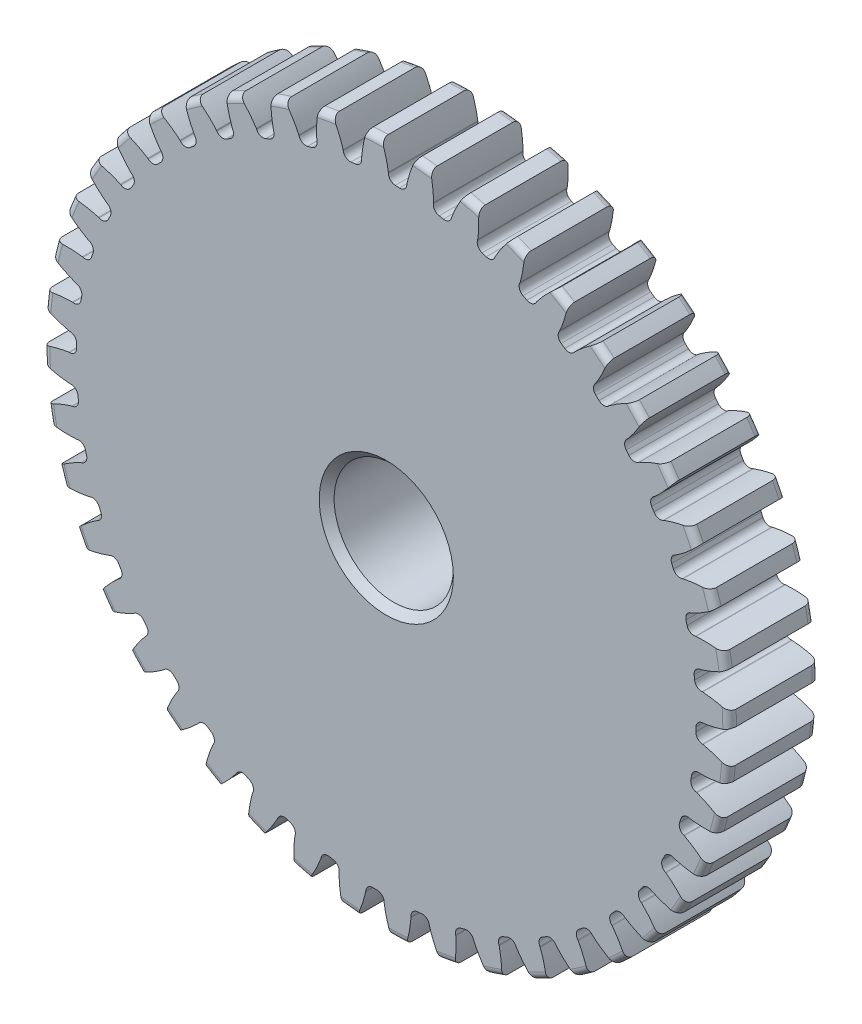
SolidWorks part; units mm, degrees
ref_plane "Front" through (0, 0, 0) normal (0, 0, 1) x (1, 0, 0)
ref_plane "Top" through (0, 0, 0) normal (0, 1, 0) x (1, 0, 0)
ref_plane "Right" through (0, 0, 0) normal (1, 0, 0) x (0, 0, -1)
sketch "Sketch1" plane through (0, 0, 0) normal (0, 0, 1) x (1, 0, 0)
  line L0 (-558.8, 0) -> (558.8, 0) construction
  circle A0 centre (0, 0) radius 18.288
  circle A1 centre (0, 0) radius 17.4625 construction
  circle A3 centre (0, 0) radius 16.5021 construction
  dimension "D1" = 1.7859
  dimension "OD" = 36.576
  dimension "Ptich Dia" = 34.925
  dimension "Root Dia" = 33.0041
  dimension "D3" = 0.8255
  dimension "Number of Teeth" = 1117.6
extrude "Boss-Extrude1" add sketch "Sketch1" against normal blind 4.7625
sketch "Sketch2" plane through (0, 0, 0) normal (1, 0, 0) x (0, 0, -1)
  line L0 (4.7625, 0) -> (11.1125, 0)
  line L1 (4.7625, 0) -> (4.7625, 7.9375)
  line L2 (4.7625, 7.9375) -> (11.1125, 7.9375)
  line L3 (11.1125, 7.9375) -> (11.1125, 0)
  point P5 (11.1125, -7.9375)
  point P6 (0, -18.288)
  point P7 (4.7625, -18.288)
  point P9 (0, 18.288)
  dimension "Face Wd" = 4.7625
  dimension "B Hub Dia" = 15.875
  dimension "D O'all Lg." = 11.1125
revolve "Revolve1" add sketch "Sketch2" angle 360 about L0
fillet "Fillet2" radius 0.3658 3 edges at (18.288, 0, -4.7625) (18.288, 0, 0) (7.9375, 0, -4.7625)
sketch "Sketch3" plane through (0, 0, 0) normal (0, 0, 1) x (1, 0, 0)
  line L0 (0, 0) -> (0, 18.288) construction
  line L1 (-4.233, 16.3678) -> (0, 17.4625)
  line L2 (-9.5921, 17.4625) -> (9.5921, 17.4625) construction
  line L3 (-9.2865, 15.0608) -> (9.2865, 19.8642) construction
  line L4 (-4.233, 16.3678) -> (0, 0) construction
  line L5 (-10.7969, 13.0096) -> (0, 0) construction
  line L6 (-10.7969, 13.0096) -> (-1.7323, 20.5325) construction
  line L7 (-2.9516, 16.6466) -> (0, 0) construction
  line L8 (-2.9516, 16.6466) -> (0.0619, 17.181) construction
  arc A0 (-4.233, 16.3678) -> (-10.7969, 13.0096) centre (0, 0) ccw
  circle A1 centre (0, 0) radius 17.4625 construction
  circle A2 centre (0, 0) radius 16.9063 construction
  arc A3 (-4.233, 16.3678) -> (-2.9516, 16.6466) centre (0, 0) cw
  circle A4 centre (0, 0) radius 18.288 construction
  point P6 (0, 17.4625)
  dimension "D1" = 4.3723
  dimension "Pressure Angle" = 14.5
  dimension "D2" = 7.4328
  dimension "D3" = 11.7797
  dimension "D4" = 1.3117
  dimension "D5" = 3.0606
sketch "Sketch4" plane through (0, 0, 0) normal (0, 0, 1) x (1, 0, 0)
  line L0 (0, 0) -> (0.6229, 17.4403) construction
  line L1 (0.1099, 16.9059) -> (0.1099, 16.5017)
  line L2 (0, 17.4625) -> (1.2458, 17.418) construction
  line L3 (1.0965, 16.8707) -> (1.0676, 16.4675)
  line L4 (0.1099, 16.5017) -> (0, 0) construction
  line L5 (0, 0) -> (0, 18.288) construction
  line L6 (-10.7969, 13.0096) -> (-1.7323, 20.5325) construction
  line L7 (-10.7969, 13.0096) -> (-1.7323, 20.5325) construction
  arc A0 (1.0676, 16.4675) -> (0.1099, 16.5017) centre (0, 0) ccw
  arc A1 (0, 17.4625) -> (1.2458, 17.418) centre (0, 0) cw construction
  circle A2 centre (0, 0) radius 17.4625 construction
  circle A3 centre (0, 0) radius 16.9063 construction
  circle A4 centre (0, 0) radius 16.5021 construction
  arc A5 (3.1927, 20.3566) -> (-1.7323, 20.5325) centre (0, 0) ccw
  spline S0 degree 2 poles (-1.7323, 20.5325) (-0.1985, 18.9305) (0.1099, 16.9059) knots 0 0 0 1 1 1
  spline S1 degree 2 poles (3.1927, 20.3566) (1.5485, 18.8681) (1.0965, 16.8707) knots 0 0 0 1 1 1
  dimension "D1" = 1.2468
extrude "Cut-Extrude1" cut sketch "Sketch4" against normal through all
fillet "Fillet1" radius 0.374 2 edges at (1.0676, 16.4675, -2.3813) (0.1099, 16.5017, -2.3813)
pattern_circular "CirPattern1" count 44 over 360 about axis through (0, 0, -4.7625) along (0, 0, 1) of "Cut-Extrude1", "Fillet1"
sketch "Sketch5" plane through (0, 0, 0) normal (0, 0, 1) x (1, 0, 0)
  circle A0 centre (0, 0) radius 3.175
  circle A1 centre (0, 0) radius 1.5875 construction
  dimension "Bore Min" = 6.35
  dimension "Bore Max" = 3.175
extrude "Cut-Extrude2" cut sketch "Sketch5" against normal through all
chamfer "Chamfer1" distance 0.3969 angle 45 3 edges at (7.9375, 0, -11.1125) (3.175, 0, 0) (3.175, 0, -11.1125)
sketch "Pitch Dia" plane through (0, 0, 0) normal (0, 0, 1) x (1, 0, 0)
  circle A0 centre (0, 0) radius 17.4625 construction
  circle A1 centre (0, 0) radius 17.4625 construction
equation "\"D1@Boss-Extrude1\" = \"Face Wd@Sketch2\""
equation "\"D2@Sketch3\" = \"D1@Sketch3\"*1.7"
equation "\"D3@Sketch3\" = \"D1@Sketch3\"+\"D2@Sketch3\"-.001"
equation "\"D4@Sketch3\" = \"D1@Sketch3\"*.3"
equation "\"D5@Sketch3\" = \"D1@Sketch3\"-\"D4@Sketch3\""
equation "\"D1@Sketch4\" = 1.5708/(\"Number of Teeth@Sketch1\"/\"Ptich Dia@Sketch1\")"
equation "\"D1@Chamfer1\" = \"B Hub Dia@Sketch2\"*.025"
equation "\"D1@CirPattern1\" = \"Number of Teeth@Sketch1\""
equation "\"D1@Fillet1\" = \"D1@Sketch4\"*.3"
equation "\"D1@Fillet2\" = \"OD@Sketch1\"*.01"
equation "\"D1@Sketch1\" = 2.250/(\"Number of Teeth@Sketch1\"/\"Ptich Dia@Sketch1\")"
